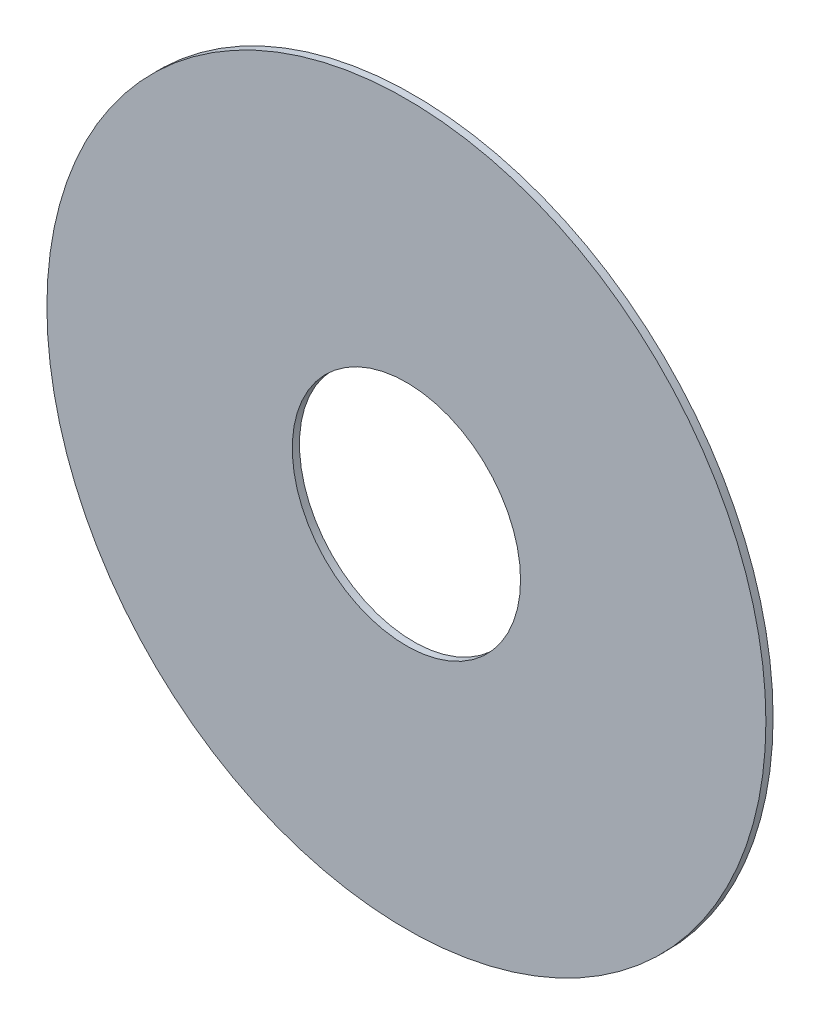
SolidWorks part; units mm, degrees
ref_plane "Plan de face" through (0, 0, 0) normal (0, 0, 1) x (1, 0, 0)
ref_plane "Plan de dessus" through (0, 0, 0) normal (0, 1, 0) x (1, 0, 0)
ref_plane "Plan de droite" through (0, 0, 0) normal (1, 0, 0) x (0, 0, -1)
sketch "Sketch1" plane through (0, 0, 0) normal (0, 0, 1) x (1, 0, 0)
  circle A0 centre (0, 0) radius 100
  circle A1 centre (0, 0) radius 31.75
  dimension "D1" = 63.5
  dimension "D2" = 200
extrude "Boss-Extrude1" add sketch "Sketch1" along normal blind 2
